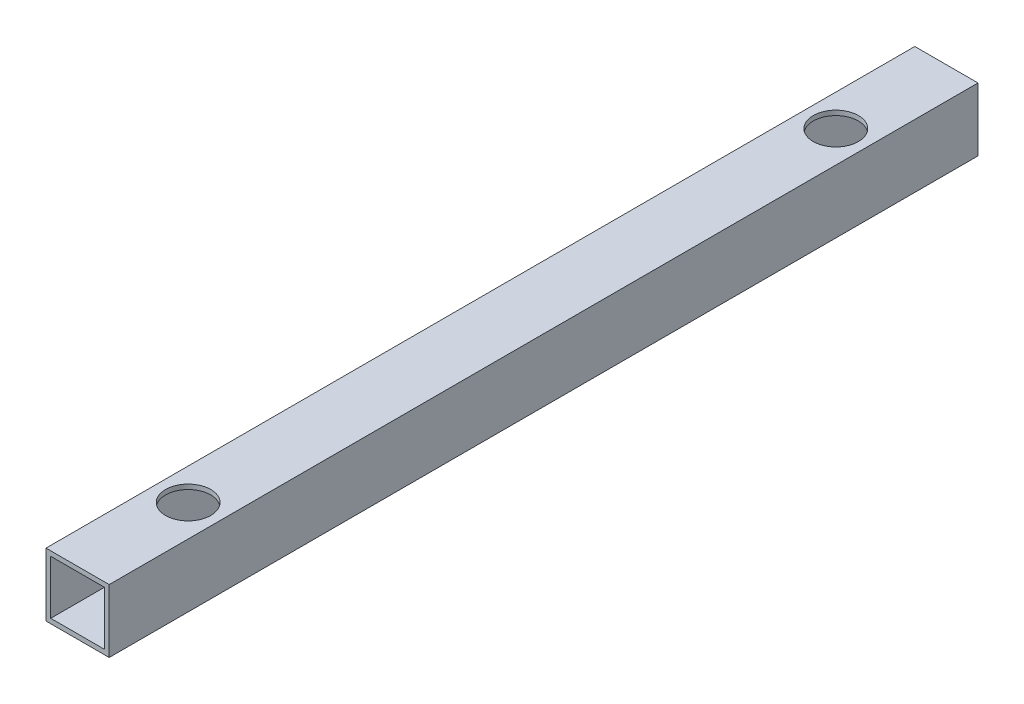
SolidWorks part; units mm, degrees
ref_plane "Front Plane" through (0, 0, 0) normal (0, 0, 1) x (1, 0, 0)
ref_plane "Top Plane" through (0, 0, 0) normal (0, 1, 0) x (1, 0, 0)
ref_plane "Right Plane" through (0, 0, 0) normal (1, 0, 0) x (0, 0, -1)
sketch "Sketch6" plane through (0, 0, 0) normal (0, 0, 1) x (1, 0, 0)
  line L0 (17, 17) -> (-17, 17)
  line L1 (20, -20) -> (-20, -20)
  line L2 (20, -20) -> (20, 20)
  line L3 (20, 20) -> (-20, 20)
  line L4 (-20, -20) -> (-20, 20)
  line L5 (20, -20) -> (-20, 20) construction
  line L6 (20, 20) -> (-20, -20) construction
  line L7 (-17, -17) -> (-17, 17)
  line L8 (17, -17) -> (-17, -17)
  line L9 (17, -17) -> (17, 17)
  point P0 (0, 0)
  dimension "D1" = 40
  dimension "D2" = 40
  dimension "D3" = 3
extrude "Boss-Extrude2" add sketch "Sketch6" along normal blind 550
sketch "Sketch8" plane through (0, 20, 0) normal (0, 1, 0) x (1, 0, 0)
  line L0 (-20, -275) -> (20, -275) construction
  line L1 (-20, -550) -> (-20, 0) construction
  line L2 (20, -550) -> (20, 0) construction
  line L4 (20, -550) -> (-20, -550) construction
  circle A0 centre (0, -480) radius 14.3
  circle A1 centre (0, -70) radius 14.3
  dimension "D1" = 28.6
  dimension "D2" = 70
extrude "Cut-Extrude2" cut sketch "Sketch8" against normal blind 10000
